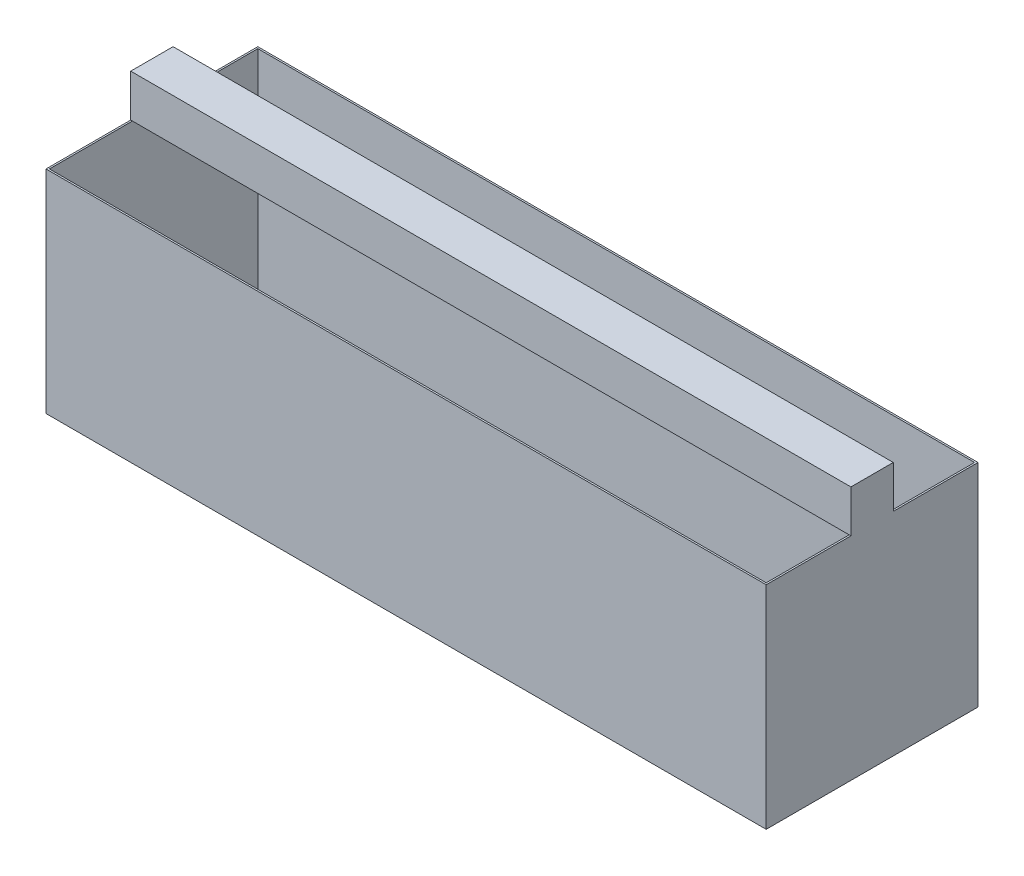
SolidWorks part; units mm, degrees
ref_plane "Front Plane" through (0, 0, 0) normal (0, 0, 1) x (1, 0, 0)
ref_plane "Top Plane" through (0, 0, 0) normal (0, 1, 0) x (1, 0, 0)
ref_plane "Right Plane" through (0, 0, 0) normal (1, 0, 0) x (0, 0, -1)
sketch "Sketch1" plane through (0, 0, 0) normal (0, 0, 1) x (1, 0, 0)
  line L1 (0, 0) -> (1700, 0)
  line L2 (0, 0) -> (0, 500)
  line L3 (0, 500) -> (1700, 500)
  line L4 (1700, 0) -> (1700, 500)
  dimension "D1" = 1700
  dimension "D2" = 500
extrude "Boss-Extrude1" add sketch "Sketch1" along normal blind 500 contours L3 L4 L1 L2
shell "Shell1" thickness 4
sketch "Sketch2" plane through (1700, 0, 0) normal (1, 0, 0) x (0, 0, -1)
  line L0 (-500, 500) -> (0, 500) construction
  line L1 (-300, 600) -> (-200, 600)
  line L2 (-300, 600) -> (-300, 500)
  line L3 (-300, 500) -> (-200, 500)
  line L4 (-200, 600) -> (-200, 500)
  point P4 (-250, 500)
  point P7 (-45.7478, 107.4635)
  dimension "D1" = 100
extrude "Boss-Extrude2" add sketch "Sketch2" against normal up to surface (1700 mm away) contours L1 L4 L3 L2 up to face at (0, 250, 250)
